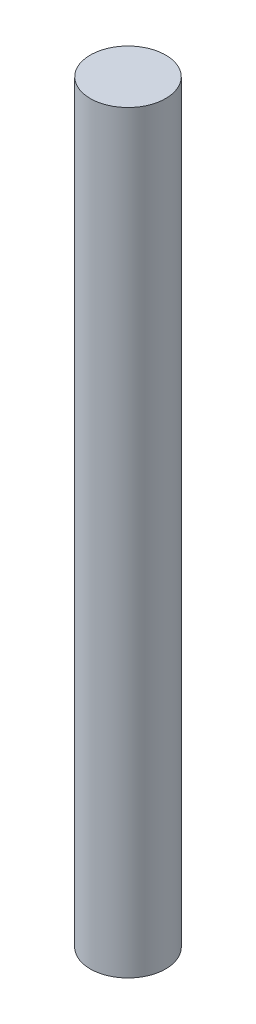
SolidWorks part; units mm, degrees
ref_plane "Face" through (0, 0, 0) normal (0, 0, 1) x (1, 0, 0)
ref_plane "Dessus" through (0, 0, 0) normal (0, 1, 0) x (1, 0, 0)
ref_plane "Droite" through (0, 0, 0) normal (1, 0, 0) x (0, 0, -1)
sketch "Esquisse1" plane through (0, 0, 0) normal (0, 1, 0) x (1, 0, 0)
  circle A0 centre (0, 0) radius 1.5
  dimension "D1" = 3
extrude "Extrusion1" add sketch "Esquisse1" along normal blind 30
